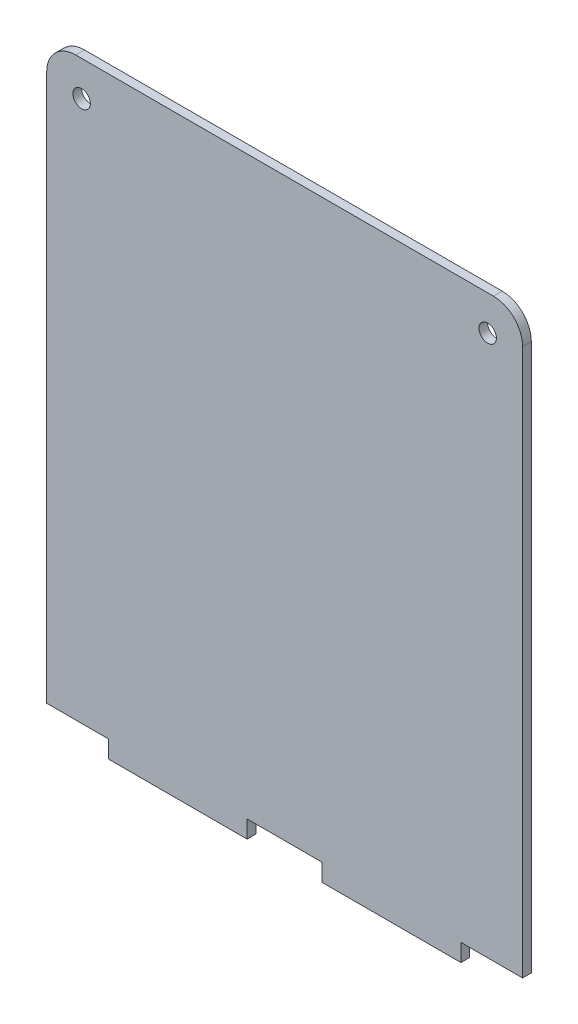
SolidWorks part; units mm, degrees
ref_plane "Front Plane" through (0, 0, 0) normal (0, 0, 1) x (1, 0, 0)
ref_plane "Top Plane" through (0, 0, 0) normal (0, 1, 0) x (1, 0, 0)
ref_plane "Right Plane" through (0, 0, 0) normal (1, 0, 0) x (0, 0, -1)
sketch "Sketch1" plane through (0, 0, 0) normal (0, 0, 1) x (1, 0, 0)
  line L1 (0, 0) -> (81.8, 0)
  line L2 (0, 0) -> (0, 102)
  line L3 (0, 102) -> (81.8, 102)
  line L4 (81.8, 0) -> (81.8, 102)
  dimension "D1" = 81.8
  dimension "D2" = 102
extrude "Boss-Extrude1" add sketch "Sketch1" along normal blind 1.5
sketch "Sketch2" plane through (0, 0, 1.5) normal (0, 0, 1) x (1, 0, 0)
  line L0 (40.9, 102) -> (40.9, 0)
  line L1 (81.8, 102) -> (0, 102) construction
  line L2 (0, 0) -> (81.8, 0) construction
  line L3 (81.8, 0) -> (81.8, 3)
  line L4 (0, 0) -> (10.6, 0)
  line L5 (0, 0) -> (0, 3)
  line L6 (0, 3) -> (10.6, 3)
  line L7 (10.6, 0) -> (10.6, 3)
  line L8 (34.455, 0) -> (47.345, 0)
  line L9 (34.455, 0) -> (34.455, 3)
  line L10 (34.455, 3) -> (47.345, 3)
  line L11 (47.345, 0) -> (47.345, 3)
  line L12 (81.8, 0) -> (71.2, 0)
  line L13 (71.2, 0) -> (71.2, 3)
  line L14 (81.8, 3) -> (71.2, 3)
  line L15 (0, 102) -> (0, 0) construction
  circle A0 centre (6, 96) radius 1.5
  circle A1 centre (75.8, 96) radius 1.5
  line M8 (0, 102) -> (0, 0)
  line M9 (0, 0) -> (81.8, 0)
  line M10 (81.8, 0) -> (81.8, 102)
  dimension "D5" = 6
  dimension "D1" = 3
  dimension "D2" = 10.6
  dimension "D3" = 12.89
  dimension "D4" = 6.445
  dimension "D6" = 6
extrude "Cut-Extrude1" cut sketch "Sketch2" against normal through all contours L7 L6 M9 M8 | L11 L10 L0 M9 | L10 L9 L0 M9 | L14 L13 M10 M9 | A0 | A1
sketch "Sketch3" plane through (0, 0, 1.5) normal (0, 0, 1) x (1, 0, 0)
  line L0 (0, 33.6536) -> (81.8, 33.6536)
  line L1 (0, 102) -> (0, 3) construction
  line L2 (81.8, 3) -> (81.8, 102) construction
  line L3 (40.9, 102) -> (40.9, 3)
  line L4 (81.8, 102) -> (0, 102) construction
  line L5 (34.455, 3) -> (47.345, 3) construction
  line L6 (35.4, 39.1536) -> (46.4, 39.1536)
  line L7 (35.4, 28.1536) -> (46.4, 28.1536)
  circle A0 centre (35.4, 33.6536) radius 5.5
  circle A1 centre (46.4, 33.6536) radius 5.5
  point P19 (40.9, 28.1536)
  point P20 (40.9, 39.1536)
  dimension "D1" = 5.5
  dimension "D2" = 11
  dimension "D3" = 68.3464
extrude "Cut-Extrude2" [suppressed] cut sketch "Sketch3" against normal through all contours L0 A0 | L0 A0 | A1 L0 | A1 L0 | A0 L7 L3 | L7 A1 L3 | L3 A1 L6 | A0 L3 L6
fillet "Fillet1" radius 5 2 edges at (81.8, 102, 0.75) (0, 102, 0.75)
